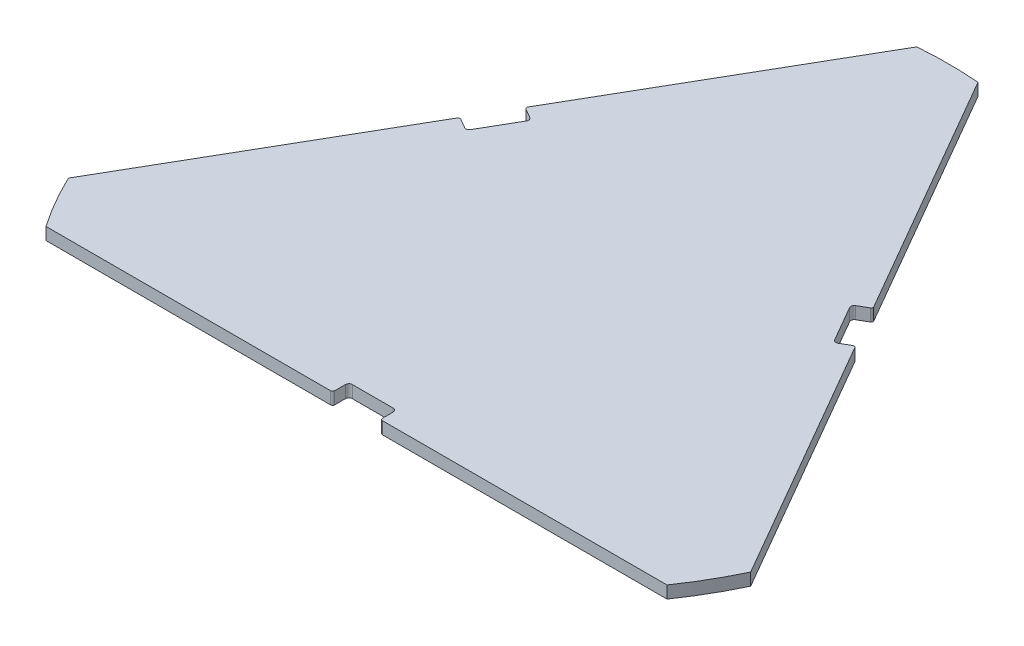
SolidWorks part; units mm, degrees
material "Polyester Resin"
ref_plane "Front Plane" through (0, 0, 0) normal (0, 0, 1) x (1, 0, 0)
ref_plane "Top Plane" through (0, 0, 0) normal (0, 1, 0) x (1, 0, 0)
ref_plane "Right Plane" through (0, 0, 0) normal (1, 0, 0) x (0, 0, -1)
sketch "Sketch1" plane through (0, 0, 0) normal (0, 1, 0) x (1, 0, 0)
  line L0 (-455.4269, -314.82) -> (-38, -314.82)
  line L1 (-35, -311.82) -> (-35, -291)
  line L2 (-35, -291) -> (35, -291)
  line L3 (35, -291) -> (35, -311.82)
  line L4 (38, -314.82) -> (455.4269, -314.82)
  line L5 (-88.1968, 57.962) -> (88.1968, 57.962) construction
  line L6 (88.1968, 57.962) -> (94.4759, 47.038) construction
  line L7 (6.3, -105.3498) -> (94.4759, 47.038) construction
  line L8 (-6.3, -105.3498) -> (6.3, -105.3498) construction
  line L9 (-94.4759, 47.038) -> (-6.3, -105.3498) construction
  line L10 (-88.1968, 57.962) -> (-94.4759, 47.038) construction
  line L11 (500.3555, -237.0012) -> (291.6421, 124.501)
  line L12 (287.544, 125.5991) -> (269.5134, 115.1891)
  line L13 (269.5134, 115.1891) -> (234.5134, 175.8109)
  line L14 (234.5134, 175.8109) -> (252.544, 186.2209)
  line L15 (253.6421, 190.319) -> (44.9287, 551.8212)
  line L16 (-44.9287, 551.8212) -> (-253.6421, 190.319)
  line L17 (-252.544, 186.2209) -> (-234.5134, 175.8109)
  line L18 (-234.5134, 175.8109) -> (-269.5134, 115.1891)
  line L19 (-269.5134, 115.1891) -> (-287.544, 125.5991)
  line L20 (-291.6421, 124.501) -> (-500.3555, -237.0012)
  arc A0 (-38, -314.82) -> (-35, -311.82) centre (-38, -311.82) ccw
  arc A1 (35, -311.82) -> (38, -314.82) centre (38, -311.82) ccw
  arc A2 (-500.3555, -237.0012) -> (-455.4269, -314.82) centre (0, 0) ccw
  arc A3 (291.6421, 124.501) -> (287.544, 125.5991) centre (289.044, 123.001) ccw
  arc A4 (252.544, 186.2209) -> (253.6421, 190.319) centre (251.044, 188.819) ccw
  arc A5 (-253.6421, 190.319) -> (-252.544, 186.2209) centre (-251.044, 188.819) ccw
  arc A6 (-287.544, 125.5991) -> (-291.6421, 124.501) centre (-289.044, 123.001) ccw
  arc A7 (44.9287, 551.8212) -> (-44.9287, 551.8212) centre (0, 0) ccw
  arc A8 (455.4269, -314.82) -> (500.3555, -237.0012) centre (0, 0) ccw
  circle A9 centre (0, -153.1749) radius 1.25 construction
  circle A10 centre (0, -243.1749) radius 1.25 construction
  circle A11 centre (-132.5456, 76.4009) radius 1.25 construction
  circle A12 centre (-210.4879, 121.4009) radius 1.25 construction
  circle A13 centre (132.5456, 76.4009) radius 1.25 construction
  circle A14 centre (210.4879, 121.4009) radius 1.25 construction
extrude "Boss-Extrude1" add sketch "Sketch1" along normal blind 18
fillet "Fillet1" radius 5 6 edges at (-234.5134, 9, -175.8109) (-269.5134, 9, -115.1891) (269.5134, 9, -115.1891) (234.5134, 9, -175.8109) (35, 9, 291) (-35, 9, 291)
